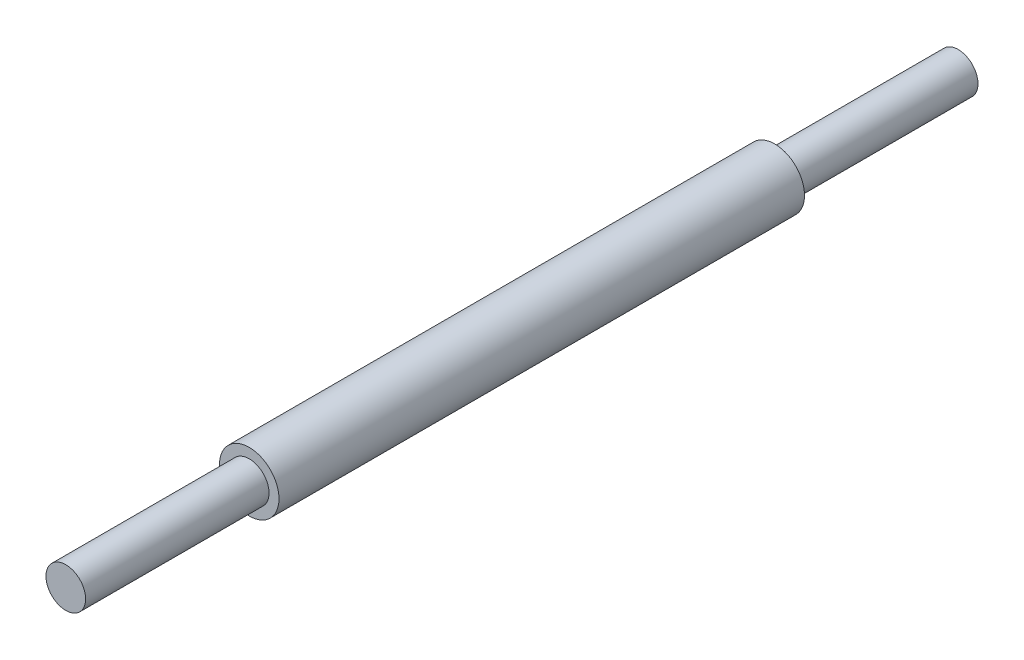
SolidWorks part; units mm, degrees
ref_plane "Front" through (0, 0, 0) normal (0, 0, 1) x (1, 0, 0)
ref_plane "Top" through (0, 0, 0) normal (0, 1, 0) x (1, 0, 0)
ref_plane "Right" through (0, 0, 0) normal (1, 0, 0) x (0, 0, -1)
sketch "Эскиз1" plane through (0, 0, 0) normal (0, 0, 1) x (1, 0, 0)
  circle A0 centre (0, 0) radius 1.5
  dimension "D1" = 3
extrude "Бобышка-Вытянуть1" add sketch "Эскиз1" along normal mid plane 26.5
sketch "Эскиз2" plane through (0, 0, 0) normal (0, 0, 1) x (1, 0, 0)
  circle A0 centre (0, 0) radius 1
  dimension "D1" = 2
extrude "Бобышка-Вытянуть2" add sketch "Эскиз2" along normal mid plane 45
